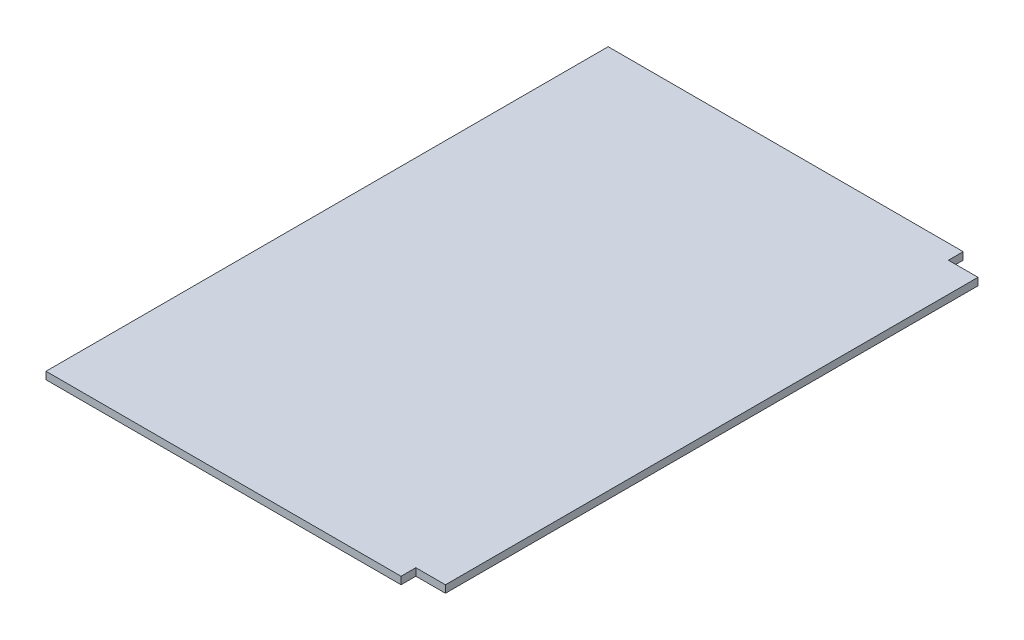
SolidWorks part; units mm, degrees
ref_plane "Front Plane" through (0, 0, 0) normal (0, 0, 1) x (1, 0, 0)
ref_plane "Top Plane" through (0, 0, 0) normal (0, 1, 0) x (1, 0, 0)
ref_plane "Right Plane" through (0, 0, 0) normal (1, 0, 0) x (0, 0, -1)
sketch "Sketch1" plane through (0, 0, 0) normal (0, 1, 0) x (1, 0, 0)
  line L0 (-457.2, 609.6) -> (457.2, 609.6) construction
  line L1 (457.2, 609.6) -> (457.2, -609.6) construction
  line L2 (0, 609.6) -> (0, 0) construction
  line L3 (0, 0) -> (457.2, 0) construction
  dimension "Width" = 914.4
  dimension "Length" = 1219.2
sketch "Sketch2" plane through (0, 0, 0) normal (1, 0, 0) x (0, 0, -1)
  line L0 (609.6, 0) -> (609.6, -12.7) construction
  dimension "Thk" = 12.7
sketch "Sketch3" plane through (0, 0, 0) normal (0, 1, 0) x (1, 0, 0)
  line L1 (-457.2, 609.6) -> (457.2, 609.6)
  line L2 (-457.2, 609.6) -> (-457.2, -609.6)
  line L3 (-457.2, -609.6) -> (457.2, -609.6)
  line L4 (457.2, 609.6) -> (457.2, -609.6)
extrude "Boss-Extrude1" add sketch "Sketch3" against normal up to vertex (12.7 mm away) up to point (0, -12.7, -609.6)
sketch "Sketch4" plane through (0, 0, 0) normal (0, 1, 0) x (1, 0, 0)
  line L3 (-457.2, 355.6) -> (203.2, 355.6)
  line L4 (203.2, -609.6) -> (203.2, 355.6)
  line L5 (-457.2, 355.6) -> (457.2, 355.6)
  line L6 (-457.2, 355.6) -> (-457.2, 609.6)
  line L7 (-457.2, 609.6) -> (457.2, 609.6)
  line L8 (457.2, 355.6) -> (457.2, 609.6)
  line L9 (203.2, 355.6) -> (457.2, 355.6)
  line L10 (203.2, 355.6) -> (203.2, -609.6)
  line L11 (203.2, -609.6) -> (457.2, -609.6)
  line L12 (457.2, 355.6) -> (457.2, -609.6)
  line M13 (-457.2, 609.6) -> (-457.2, -609.6)
  line M14 (-457.2, -609.6) -> (457.2, -609.6)
  line M15 (457.2, -609.6) -> (457.2, 609.6)
  line M16 (457.2, 609.6) -> (-457.2, 609.6)
extrude "Cut-Extrude1" cut sketch "Sketch4" against normal up to surface (12.7 mm away) contours L3 L5 M15 M16 M13 | L5 L4 M14 M15 up to face at (0, -12.7, 0)
sketch "Sketch5" plane through (0, 0, 0) normal (0, 1, 0) x (1, 0, 0)
  line L1 (203.2, 355.6) -> (152.4, 355.6)
  line L2 (203.2, 355.6) -> (203.2, 330.2)
  line L3 (203.2, 330.2) -> (152.4, 330.2)
  line L4 (152.4, 355.6) -> (152.4, 330.2)
  line L5 (203.2, -609.6) -> (152.4, -609.6)
  line L6 (203.2, -609.6) -> (203.2, -584.2)
  line L7 (203.2, -584.2) -> (152.4, -584.2)
  line L8 (152.4, -609.6) -> (152.4, -584.2)
  dimension "D1" = 25.4
  dimension "D2" = 50.8
  dimension "D3" = 25.4
  dimension "D4" = 50.8
extrude "Cut-Extrude2" cut sketch "Sketch5" against normal up to surface (12.7 mm away) up to face at (-127, -12.7, 127)
